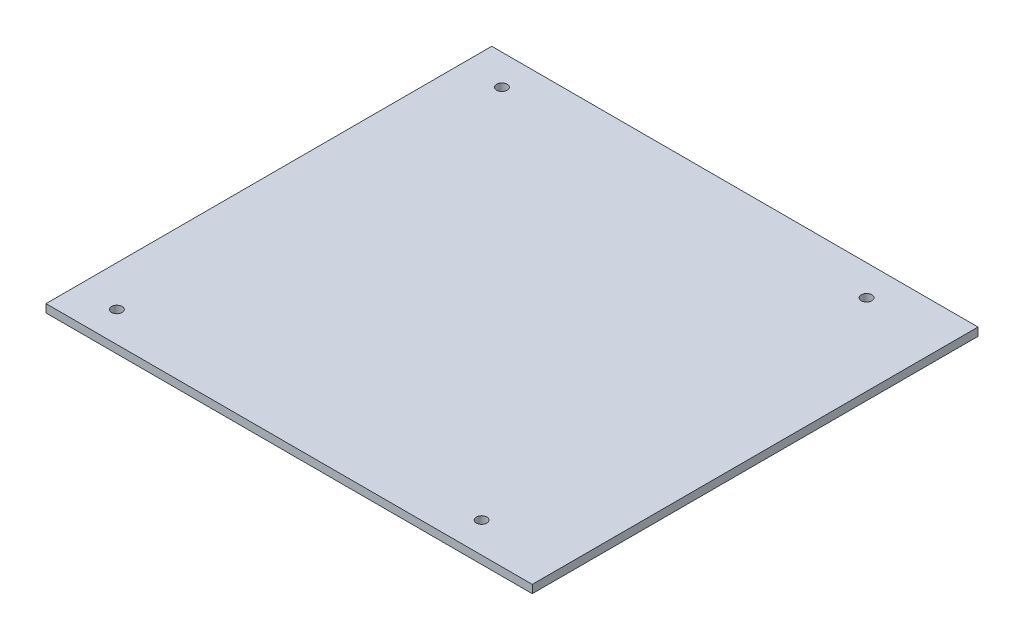
SolidWorks part; units mm, degrees
ref_plane "Front Plane" through (0, 0, 0) normal (0, 0, 1) x (1, 0, 0)
ref_plane "Top Plane" through (0, 0, 0) normal (0, 1, 0) x (1, 0, 0)
ref_plane "Right Plane" through (0, 0, 0) normal (1, 0, 0) x (0, 0, -1)
sketch "Sketch1" plane through (0, 0, 0) normal (0, 1, 0) x (1, 0, 0)
  line L1 (76.2, -69.85) -> (-76.2, -69.85)
  line L2 (76.2, -69.85) -> (76.2, 69.85)
  line L3 (76.2, 69.85) -> (-76.2, 69.85)
  line L4 (-76.2, -69.85) -> (-76.2, 69.85)
  line L5 (76.2, -69.85) -> (-76.2, 69.85) construction
  line L6 (76.2, 69.85) -> (-76.2, -69.85) construction
  point P0 (0, 0)
  dimension "D1" = 139.7
  dimension "D2" = 152.4
extrude "Boss-Extrude1" add sketch "Sketch1" along normal blind 2.54
hole_wizard "M4x0.7 Tapped Hole1" positions "Sketch3" profile "Sketch2" tap size "M4x0.7" standard "ANSI Metric"
sketch "Sketch3" plane through (0, 2.54, 0) normal (0, 1, 0) x (1, 0, 0)
  line L0 (-63.5, -60.325) -> (-63.5, 60.325) construction
  line L2 (50.8, 60.325) -> (50.8, -60.325) construction
  point P0 (-63.5, 60.325)
  point P2 (-63.5, -60.325)
  point P4 (50.8, -60.325)
  point P6 (50.8, 60.325)
  point P16 (-63.5, 0)
  dimension "D1" = 120.65
  dimension "D2" = 63.5
  dimension "D3" = 50.8
sketch "Sketch2" plane through (-63.5, 2.54, -60.325) normal (1, 0, 0) x (0, 0, 1)
  line L0 (0, 0) -> (0, 9.906)
  line L1 (0, 9.906) -> (1.65, 9.906)
  line L2 (1.65, 9.906) -> (1.65, 0)
  line L5 (1.65, 0) -> (0, 0)
  line L10 (0, 9.906) -> (-1.65, 9.906) construction
  line L11 (0, -6.35) -> (0, 107.95) construction
  dimension "Tap Drill Dia." = 3.3
  dimension "Tap Drill Depth" = 9.906
  dimension "Drill Angle" = 180
cosmetic thread "Hole Thread1" parameters "D1"=2.54, "D2"=4
cosmetic thread "Hole Thread2" parameters "D1"=2.54, "D2"=4
cosmetic thread "Hole Thread3" parameters "D1"=2.54, "D2"=4
cosmetic thread "Hole Thread4" parameters "D1"=2.54, "D2"=4
